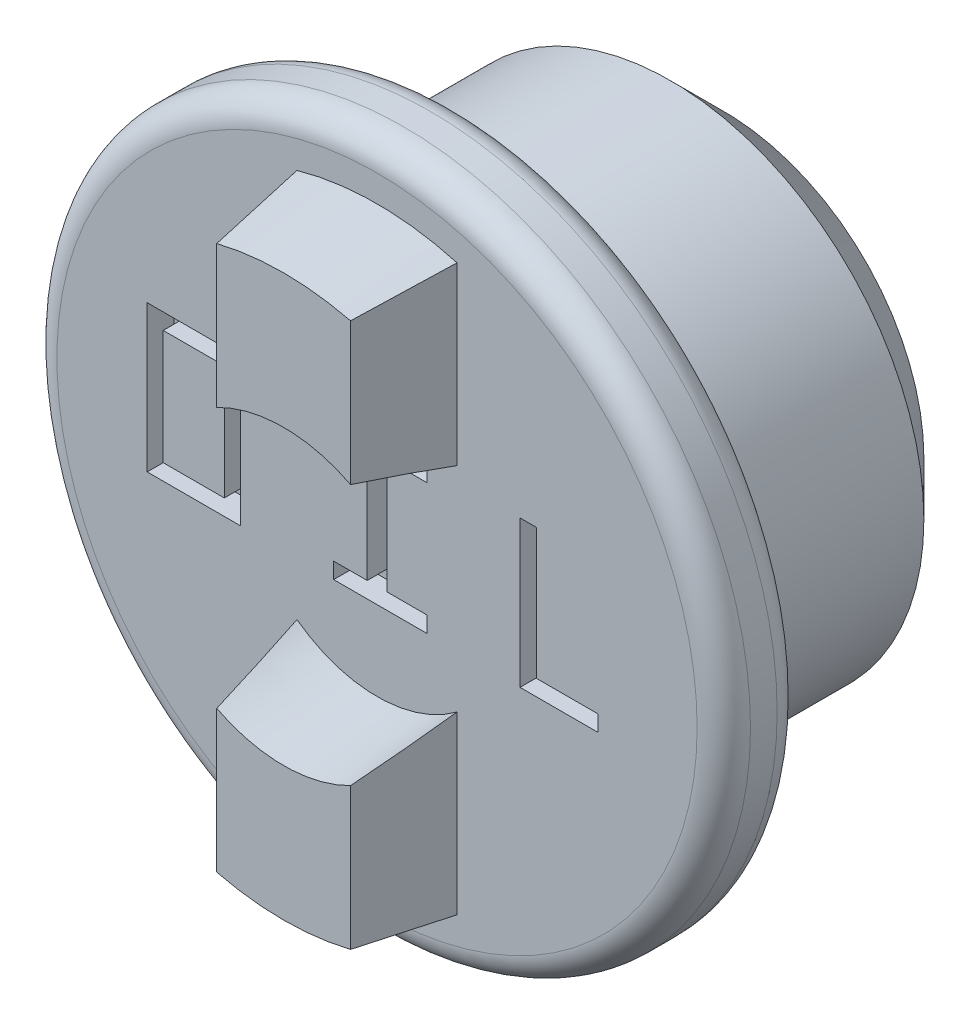
SolidWorks part; units mm, degrees
ref_plane "Front Plane" through (0, 0, 0) normal (0, 0, 1) x (1, 0, 0)
ref_plane "Top Plane" through (0, 0, 0) normal (0, 1, 0) x (1, 0, 0)
ref_plane "Right Plane" through (0, 0, 0) normal (1, 0, 0) x (0, 0, -1)
sketch "Sketch1" plane through (0, 0, 0) normal (0, 0, 1) x (1, 0, 0)
  circle A0 centre (0, 0) radius 9.5
  dimension "D1" = 19
extrude "Boss-Extrude1" add sketch "Sketch1" along normal blind 10
chamfer "Chamfer1" distance 2 angle 45 1 edges at (9.5, 0, 0)
sketch "Sketch2" plane through (0, 0, 10) normal (0, 0, 1) x (1, 0, 0)
  circle A0 centre (0, 0) radius 13
  dimension "D1" = 26
extrude "Boss-Extrude2" add sketch "Sketch2" along normal blind 3
sketch "Sketch4" plane through (0, 0, 13) normal (0, 0, 1) x (1, 0, 0)
  line L0 (0, 13.5071) -> (0, 5) construction
  line L1 (3, 10.583) -> (3, 4)
  line L2 (-3, 10.583) -> (-3, 4)
  line L3 (3, -4) -> (3, -10.583)
  line L4 (0, -5) -> (0, -14.5643) construction
  line L5 (-3, -4) -> (-3, -10.583)
  arc A1 (-3, -4) -> (3, -4) centre (0, 0) ccw
  circle A2 centre (0, 0) radius 5
  circle A3 centre (0, 0) radius 11
  arc A4 (3, 10.583) -> (-3, 10.583) centre (0, 0) ccw
  arc A5 (3, 4) -> (-3, 4) centre (0, 0) ccw
  arc A6 (-3, -10.583) -> (3, -10.583) centre (0, 0) ccw
  dimension "D3" = 6
  dimension "D1" = 2
  dimension "D2" = 8
extrude "Boss-Extrude3" add sketch "Sketch4" along normal blind 3.5 draft 8
sketch "Sketch5" plane through (0, 0, 16.5) normal (0, 0, 1) x (1, 0, 0)
  line L14 (-17.9352, 0) -> (20.3888, 0) construction
fillet "Fillet1" radius 1 2 edges at (13, 0, 10) (13, 0, 13)
sketch "Sketch3" plane through (0, 0, 13) normal (0, 0, 1) x (1, 0, 0)
  line L0 (-14.7284, 0) -> (19.3583, 0) construction
  line L1 (-1.6251, -2.0139) -> (-1.6251, -1.4139)
  line L2 (-1.6251, 3.4803) -> (1.8749, 3.4803)
  line L21 (1.8749, 3.4803) -> (1.8749, 2.8803)
  line L26 (1.8749, -2.0139) -> (-1.6251, -2.0139)
  line L31 (0.3676, 2.8803) -> (0.3676, -1.4139)
  line L33 (0.3676, 2.8803) -> (1.8749, 2.8803)
  line L35 (0.3676, -1.4139) -> (1.8749, -1.4139)
  line L36 (5.3598, 3.4803) -> (5.3598, -1.4197)
  line L39 (8.2749, -1.4197) -> (5.9749, -1.4197)
  line L46 (8.2749, -2.0197) -> (5.3598, -2.0197)
  line L47 (5.3598, -2.0197) -> (5.3598, -1.4197)
  line L48 (-8.6155, 3.4803) -> (-8.6155, -2.0139)
  line L49 (-8.6155, -2.0139) -> (-5.1251, -2.0139)
  line L52 (-8.6155, 3.4803) -> (-5.1251, 3.4803)
  line L55 (-8.0155, -1.4139) -> (-5.7251, -1.4139)
  line L56 (-8.0155, 2.8803) -> (-8.0155, -1.4139)
  line L57 (-8.0155, 2.8803) -> (-5.7251, 2.8803)
  line L58 (-5.1251, 3.4803) -> (-5.1251, 2.8803)
  line L60 (-3, 10.583) -> (-3, 4) construction
  line L61 (-5.1251, 0.584) -> (-5.5946, -0.8283) construction
  line L62 (-5.7251, -1.4139) -> (-5.7251, -1.4139) construction
  line L63 (-5.7251, -1.4139) -> (-5.7251, 2.8803)
  line L65 (-8.0155, 2.8803) -> (-5.1251, 2.8803) construction
  line L66 (-1.6251, 2.8803) -> (-0.3676, 2.8803)
  line L67 (-1.6251, -1.4139) -> (-0.3676, -1.4139)
  line L68 (-0.3676, 2.8803) -> (-0.3676, -1.4139)
  line L70 (0, 4.8091) -> (0, -4.0672) construction
  line L71 (1.8749, -1.4139) -> (1.8749, -2.0139)
  line L72 (-1.6251, 2.8803) -> (-1.6251, 3.4803)
  line L73 (-5.1251, 2.8803) -> (-5.1251, -2.0139)
  line L80 (5.9749, 3.4803) -> (5.9749, -1.4197)
  line L81 (8.2749, -1.4197) -> (8.2749, -2.0197)
  line L82 (5.3598, 3.4803) -> (5.9749, 3.4803)
  line L84 (3, 4) -> (3, 10.583) construction
  line L85 (-5.1251, -2.0139) -> (-5.1251, 0.584) construction
  line L86 (-5.7251, -1.4139) -> (-5.7251, -1.4139) construction
  dimension "D4" = 2.9749
  dimension "D5" = 0.6
  dimension "D1" = 2.3598
  dimension "D2" = 0.6
  dimension "D6" = 5.2749
  dimension "D7" = 1.1251
  dimension "D8" = 3.5
  dimension "D9" = 2.6324
  dimension "D10" = 8.7251
  dimension "D11" = 11.0155
  dimension "D12" = 11.6155
  dimension "D13" = 7.1027
  dimension "D3" = 3.5
  dimension "D14" = 7.7027
  dimension "D16" = 11.9969
  dimension "D17" = 12.0027
extrude "Cut-Extrude1" cut sketch "Sketch3" against normal blind 1
